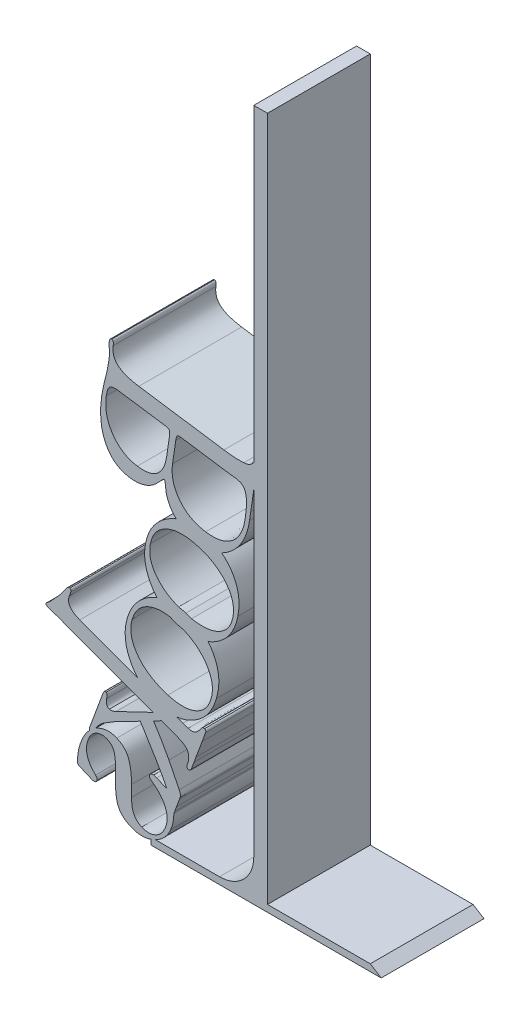
SolidWorks part; units mm, degrees
ref_plane "Plan de face" through (0, 0, 0) normal (0, 0, 1) x (1, 0, 0)
ref_plane "Plan de dessus" through (0, 0, 0) normal (0, 1, 0) x (1, 0, 0)
ref_plane "Plan de droite" through (0, 0, 0) normal (1, 0, 0) x (0, 0, -1)
sketch "Esquisse1" plane through (0, 0, 0) normal (0, 0, 1) x (1, 0, 0)
  line L0 (0, 0) -> (37.189, 0)
  line L1 (37.189, 0) -> (34, 2)
  line L2 (34, 2) -> (4, 2)
  line L3 (4, 2) -> (4, 202)
  line L4 (4, 202) -> (0, 202)
  line L5 (0, 202) -> (0, 2)
  line L6 (0, 2) -> (-30, 2)
  line L7 (-30, 2) -> (-30, 0)
  line L8 (-30, 0) -> (0, 0)
  dimension "D1" = 2
  dimension "D2" = 4
  dimension "D3" = 2
  dimension "100" = 200
  dimension "D4" = 30
  dimension "D5" = 30
sketch "Esquisse3" plane through (0, 0, 0) normal (0, 0, 1) x (1, 0, 0)
  line L3 (-29.24, -3.4331) -> (4, 68.1983) construction
  line L6 (4, 68.1983) -> (4, 164.7761) construction
  line L8 (4, 2) -> (4, 202) construction
  spline S0 degree 2 poles (-29.24, -3.4331) (4, 68.1983) (4, 164.7761) knots 0 0 0 1 1 1 construction
  text T0 "Books" font "Goudy Old Style" height 45
  point P0 (4, 164.7761)
extrude "Boss.-Extru.1" add sketch "Esquisse1" along normal blind 30
extrude "Boss.-Extru.2" add sketch "Esquisse3" along normal blind 30
fillet "Congé1" radius 10 1 edges at (0, 2, 15)
